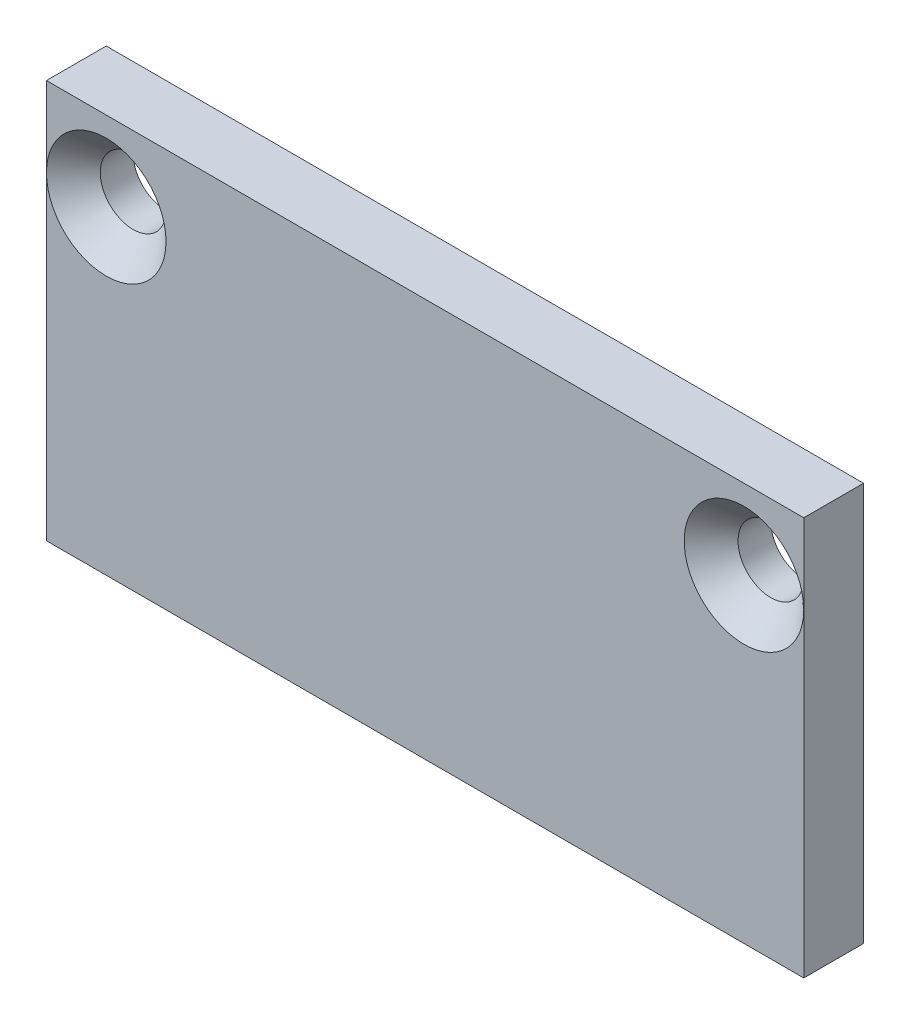
SolidWorks part; units mm, degrees
material "PTFE (general)"
ref_plane "Front Plane" through (0, 0, 0) normal (0, 0, 1) x (1, 0, 0)
ref_plane "Top Plane" through (0, 0, 0) normal (0, 1, 0) x (1, 0, 0)
ref_plane "Right Plane" through (0, 0, 0) normal (1, 0, 0) x (0, 0, -1)
sketch "Sketch1" plane through (0, 0, 0) normal (0, 0, 1) x (1, 0, 0)
  line L1 (-19, 0) -> (19, 0)
  line L2 (-19, 0) -> (-19, 20)
  line L3 (-19, 20) -> (19, 20)
  line L4 (19, 0) -> (19, 20)
  dimension "D1" = 20
  dimension "D2" = 38
extrude "Boss-Extrude1" add sketch "Sketch1" along normal blind 3
hole_wizard "CSK for M3 Flat Head Machine Screw1" positions "Sketch3" profile "Sketch2" countersink size "M3" standard "Ansi Metric" end condition through all
sketch "Sketch3" plane through (0, 0, 3) normal (0, 0, 1) x (1, 0, 0)
  line L0 (-16, 16) -> (16, 16) construction
  line L2 (19, 20) -> (-19, 20) construction
  point P0 (-16, 16)
  point P1 (16, 16)
  dimension "D1" = 4
  dimension "D2" = 16
  dimension "D3" = 32
sketch "Sketch2" plane through (-16, 16, 3) normal (1, 0, 0) x (0, -1, 0)
  line L0 (0, 0) -> (0, 3)
  line L1 (0, 3) -> (1.65, 3)
  line L2 (1.65, 3) -> (1.65, 1.35)
  line L3 (1.65, 1.35) -> (3, 0)
  line L5 (3, 0) -> (0, 0)
  line L6 (-1.65, 1.35) -> (-3, 0) construction
  line L11 (0, -6.35) -> (0, 107.95) construction
  dimension "Thru Hole Dia." = 3.3
  dimension "Thru Hole Depth" = 3
  dimension "Near C'Sink Dia." = 6
  dimension "Near C'Sink Angle" = 90
